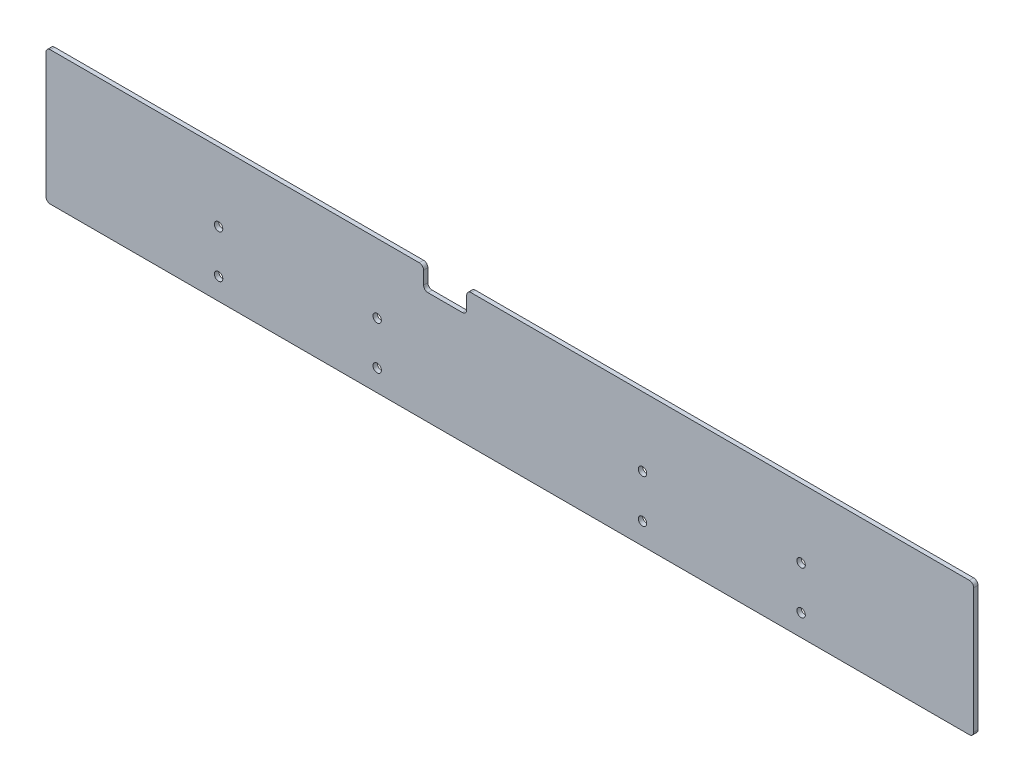
SolidWorks part; units mm, degrees
ref_plane "Front Plane" through (0, 0, 0) normal (0, 0, 1) x (1, 0, 0)
ref_plane "Top Plane" through (0, 0, 0) normal (0, 1, 0) x (1, 0, 0)
ref_plane "Right Plane" through (0, 0, 0) normal (1, 0, 0) x (0, 0, -1)
sketch "Sketch1" plane through (0, 0, 0) normal (0, 0, 1) x (1, 0, 0)
  line L0 (-161.9059, 17.7035) -> (73.0941, 17.7035)
  line L1 (-356.9059, 17.7035) -> (-181.9059, 17.7035)
  line L2 (-356.9059, 17.7035) -> (-356.9059, -44.2965)
  line L3 (-356.9059, -44.2965) -> (73.0941, -44.2965)
  line L4 (73.0941, 17.7035) -> (73.0941, -44.2965)
  line L6 (-181.9059, 17.7035) -> (-181.9059, 7.7035)
  line L7 (-181.9059, 7.7035) -> (-161.9059, 7.7035)
  line L8 (-161.9059, 17.7035) -> (-161.9059, 7.7035)
  line L9 (-203.4059, -14.2965) -> (-80.4059, -14.2965) construction
  line L10 (-203.4059, -34.2965) -> (-80.4059, -34.2965) construction
  circle A0 centre (-80.4059, -14.2965) radius 1.95
  circle A1 centre (-80.4059, -34.2965) radius 1.95
  circle A2 centre (-203.4059, -14.2965) radius 1.95
  circle A3 centre (-203.4059, -34.2965) radius 1.95
  dimension "D3" = 123
  dimension "D4" = 20
  dimension "D1" = 430
  dimension "D2" = 62
  dimension "D5" = 10
  dimension "D6" = 153.5
  dimension "D7" = 20
  dimension "D8" = 10
  dimension "D9" = 175
extrude "Boss-Extrude1" add sketch "Sketch1" along normal blind 2
fillet "Fillet1" radius 2 8 edges at (73.0941, -44.2965, 1) (-356.9059, -44.2965, 1) (-356.9059, 17.7035, 1) (-181.9059, 7.7035, 1) (-181.9059, 17.7035, 1) (-161.9059, 7.7035, 1) (-161.9059, 17.7035, 1) (73.0941, 17.7035, 1)
sketch "Sketch2" plane through (0, 0, 2) normal (0, 0, 1) x (1, 0, 0)
  line L0 (-354.9059, -44.2965) -> (71.0941, -44.2965) construction
  line L1 (-356.9059, 15.7035) -> (-356.9059, -42.2965) construction
  line L2 (73.0941, -42.2965) -> (73.0941, 15.7035) construction
  circle A0 centre (-276.9059, -14.2965) radius 1.95
  circle A1 centre (-276.9059, -34.2965) radius 1.95
  circle A2 centre (-6.9059, -14.2965) radius 1.95
  circle A3 centre (-6.9059, -34.2965) radius 1.95
  dimension "D1" = 20
  dimension "D2" = 10
  dimension "D3" = 80
  dimension "D4" = 80
  dimension "D5" = 20
  dimension "D6" = 10
extrude "Cut-Extrude1" cut sketch "Sketch2" against normal blind 10
